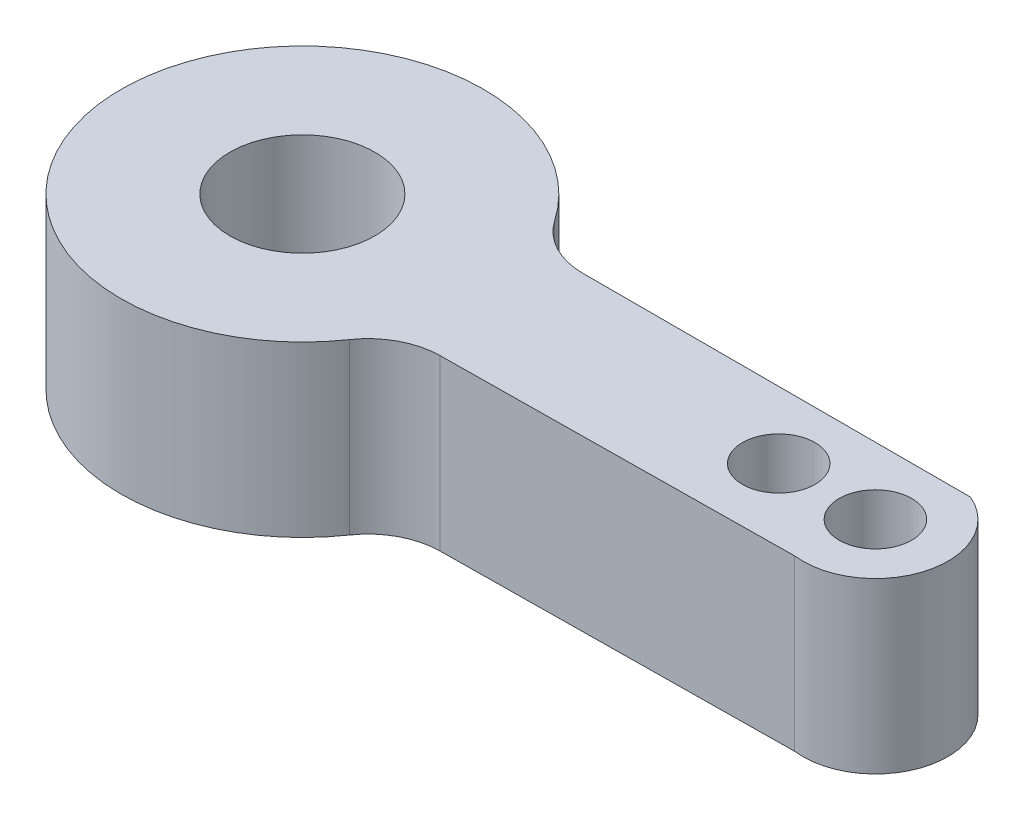
SolidWorks part; units mm, degrees
ref_plane "Front Plane" through (0, 0, 0) normal (0, 0, 1) x (1, 0, 0)
ref_plane "Top Plane" through (0, 0, 0) normal (0, 1, 0) x (1, 0, 0)
ref_plane "Right Plane" through (0, 0, 0) normal (1, 0, 0) x (0, 0, -1)
sketch "Sketch4" plane through (0, 0, 0) normal (0, 1, 0) x (1, 0, 0)
  line L0 (0, 0) -> (62.7277, 0) construction
  line L1 (6.891, 2.9604) -> (24.6694, 2.9604)
  line L2 (6.891, -2.9604) -> (23.1421, -2.7809)
  arc A0 (0, 7.5) -> (0, -7.5) centre (0, 0) ccw
  arc A1 (0, 7.5) -> (6.891, 2.9604) centre (0, 0) cw
  arc A2 (0, -7.5) -> (6.891, -2.9604) centre (0, 0) ccw
  arc A3 (24.6694, 2.9604) -> (23.1421, -2.7809) centre (23.5, 0.1977) cw
  circle A4 centre (23.5, 0.1977) radius 1.5
  circle A5 centre (19.5, 0.1977) radius 1.5
  circle A6 centre (0, 0) radius 3
  dimension "D1" = 19.5
  dimension "D3" = 15
  dimension "D4" = 4
  dimension "D5" = 3
extrude "Boss-Extrude1" add sketch "Sketch4" along normal blind 7
fillet "Fillet1" radius 3 2 edges at (6.891, 3.5, 2.9604) (6.891, 3.5, -2.9604)
